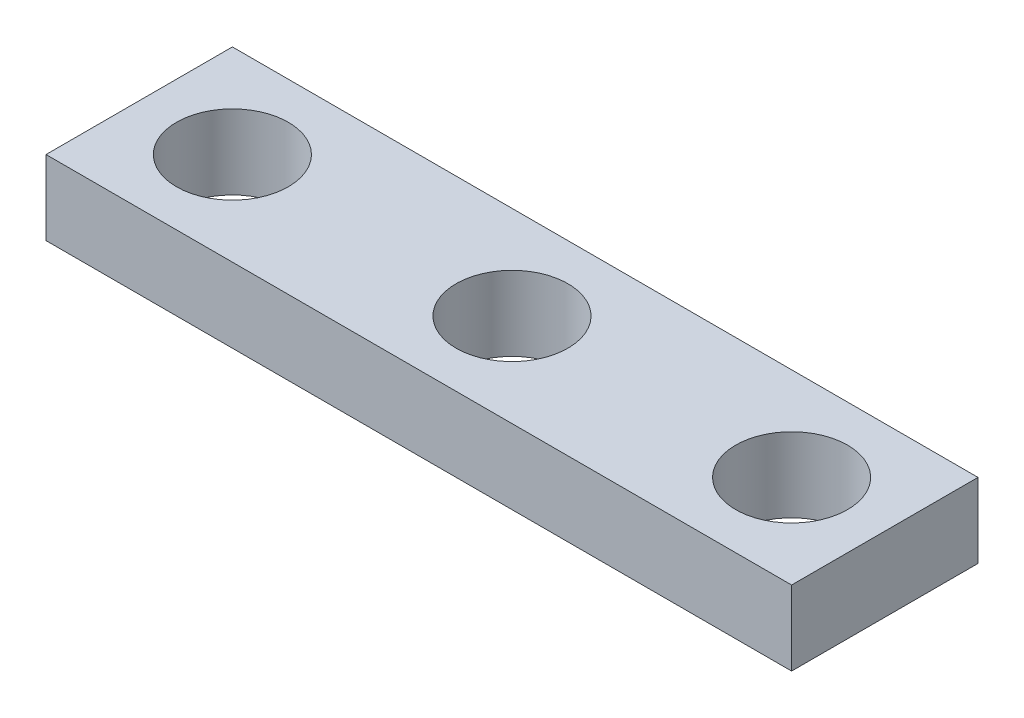
SolidWorks part; units mm, degrees
ref_plane "Front Plane" through (0, 0, 0) normal (0, 0, 1) x (1, 0, 0)
ref_plane "Top Plane" through (0, 0, 0) normal (0, 1, 0) x (1, 0, 0)
ref_plane "Right Plane" through (0, 0, 0) normal (1, 0, 0) x (0, 0, -1)
sketch "Sketch1" plane through (0, 0, 0) normal (0, 1, 0) x (1, 0, 0)
  line L0 (0, -1.0915) -> (0, 0.8269) construction
  line L1 (12.7, 3.175) -> (-12.7, 3.175)
  line L2 (-12.7, 3.175) -> (-12.7, -3.175)
  line L3 (-12.7, -3.175) -> (12.7, -3.175)
  line L4 (-9.525, 0) -> (-9.525, 3.175) construction
  line L5 (-9.525, 0) -> (-9.525, -3.175) construction
  line L6 (-9.525, 0) -> (-12.7, 0) construction
  line L7 (9.525, 0) -> (12.7, 0) construction
  line L8 (9.525, 0) -> (9.525, -3.175) construction
  line L9 (9.525, 0) -> (9.525, 3.175) construction
  line L10 (12.7, 3.175) -> (12.7, -3.175)
  circle A0 centre (-9.525, 0) radius 1.905
  circle A1 centre (9.525, 0) radius 1.905
  circle A2 centre (0, 0) radius 1.905
  point P18 (0, -3.175)
  point P19 (0, 3.175)
  dimension "D1" = 3.81
  dimension "D2" = 6.35
  dimension "D3" = 9.525
extrude "Boss-Extrude1" add sketch "Sketch1" along normal blind 2.54
